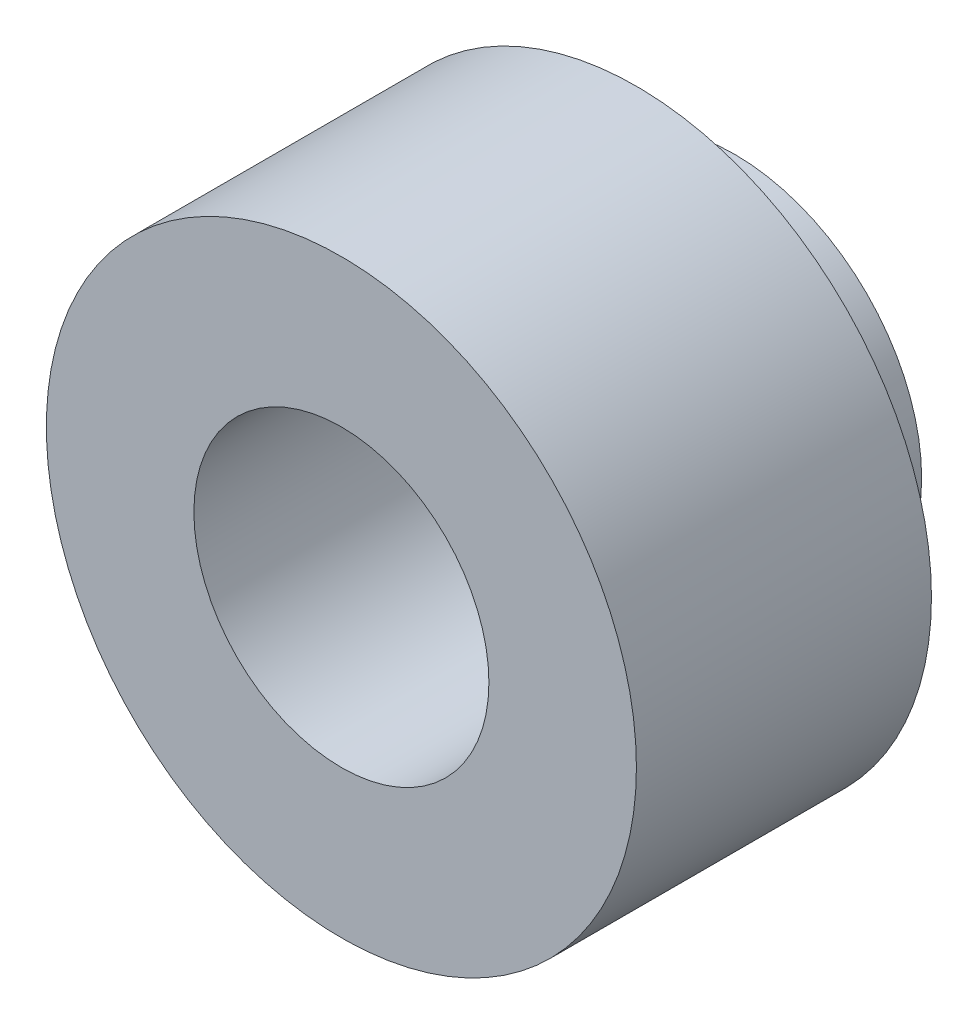
SolidWorks part; units mm, degrees
ref_plane "Front Plane" through (0, 0, 0) normal (0, 0, 1) x (1, 0, 0)
ref_plane "Top Plane" through (0, 0, 0) normal (0, 1, 0) x (1, 0, 0)
ref_plane "Right Plane" through (0, 0, 0) normal (1, 0, 0) x (0, 0, -1)
sketch "Sketch1" plane through (0, 0, 0) normal (0, 0, 1) x (1, 0, 0)
  circle A0 centre (0, 0) radius 3.75
  circle A1 centre (0, 0) radius 1.875
  dimension "D1" = 7.5
  dimension "D2" = 3.75
extrude "Boss-Extrude1" add sketch "Sketch1" along normal blind 3.75
sketch "Sketch2" plane through (0, 0, 0) normal (0, 0, -1) x (-1, 0, 0)
  circle A0 centre (0, 0) radius 1.875
  circle A1 centre (0, 0) radius 2.375
  dimension "D1" = 4.75
extrude "Boss-Extrude2" add sketch "Sketch2" along normal blind 1.25 contours A1 | A0
